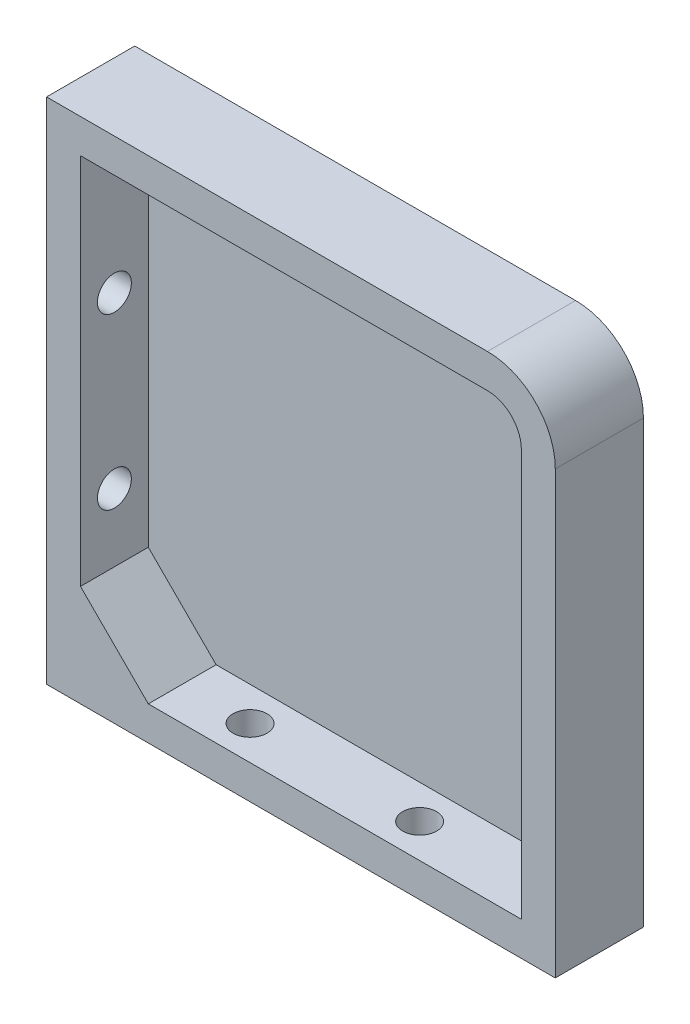
SolidWorks part; units mm, degrees
ref_plane "Plan de face" through (0, 0, 0) normal (0, 0, 1) x (1, 0, 0)
ref_plane "Plan de dessus" through (0, 0, 0) normal (0, 1, 0) x (1, 0, 0)
ref_plane "Plan de droite" through (0, 0, 0) normal (1, 0, 0) x (0, 0, -1)
sketch "Esquisse1" plane through (0, 0, 0) normal (0, 0, 1) x (1, 0, 0)
  line L1 (-20.8816, 33.7284) -> (44.1184, 33.7284)
  line L2 (-20.8816, 33.7284) -> (-20.8816, -41.2716)
  line L3 (-20.8816, -41.2716) -> (54.1184, -41.2716)
  line L4 (54.1184, 23.7284) -> (54.1184, -41.2716)
  arc A0 (44.1184, 33.7284) -> (54.1184, 23.7284) centre (44.1184, 23.7284) cw
  point P6 (54.1184, 33.7284)
  dimension "D3" = 10
  dimension "D1" = 75
  dimension "D2" = 75
extrude "Boss.-Extru.1" add sketch "Esquisse1" along normal blind 13
shell "Coque1" thickness 5
sketch "Esquisse2" plane through (-20.8816, 0, 0) normal (-1, 0, 0) x (0, 0, 1)
  line L0 (13, 33.7284) -> (13, -41.2716) construction
  line L1 (13, 33.7284) -> (0, 33.7284) construction
  line L2 (13, -41.2716) -> (0, -41.2716) construction
  circle A0 centre (8, 8.7284) radius 2.5
  circle A1 centre (8, -16.2716) radius 2.5
  dimension "D1" = 5
  dimension "D2" = 5
  dimension "D3" = 5
  dimension "D4" = 5
  dimension "D5" = 25
  dimension "D6" = 25
extrude "Enlèv. mat.-Extru.1" cut sketch "Esquisse2" against normal up to surface (5 mm away) contours A1 | A0 up to face at (-15.8816, -3.7716, 8)
sketch "Esquisse3" plane through (0, -41.2716, 0) normal (0, -1, 0) x (1, 0, 0)
  line L0 (-20.8816, 13) -> (54.1184, 13) construction
  line L2 (54.1184, 13) -> (54.1184, 0) construction
  line L3 (-20.8816, 13) -> (-20.8816, 0) construction
  circle A0 centre (4.1184, 8) radius 2.5
  circle A1 centre (29.1184, 8) radius 2.5
  dimension "D1" = 5
  dimension "D2" = 5
  dimension "D3" = 5
  dimension "D4" = 5
  dimension "D5" = 25
  dimension "D6" = 25
extrude "Enlèv. mat.-Extru.2" cut sketch "Esquisse3" against normal up to surface (5 mm away) up to face at (16.6184, -36.2716, 8)
sketch "Esquisse4" plane through (0, 0, 3) normal (0, 0, 1) x (1, 0, 0)
  line L0 (-15.8816, -26.2716) -> (-5.8816, -36.2716)
  line L1 (-15.8816, 28.7284) -> (-15.8816, -36.2716) construction
  line L2 (-15.8816, -36.2716) -> (49.1184, -36.2716) construction
  line L3 (-5.8816, -36.2716) -> (-15.8816, -36.2716)
  line L4 (-15.8816, -36.2716) -> (-15.8816, -26.2716)
  dimension "D1" = 10
  dimension "D2" = 10
extrude "Boss.-Extru.2" add sketch "Esquisse4" along normal up to surface (10 mm away) up to face at (22.5326, 2.1427, 13)
